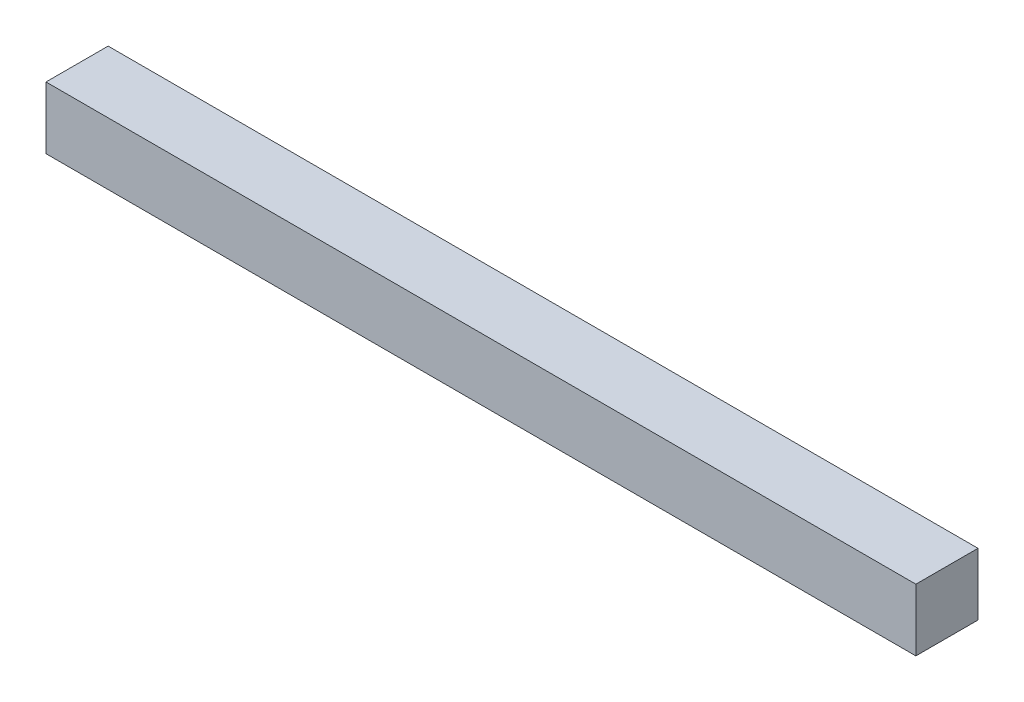
SolidWorks part; units mm, degrees
ref_plane "Front Plane" through (0, 0, 0) normal (0, 0, 1) x (1, 0, 0)
ref_plane "Top Plane" through (0, 0, 0) normal (0, 1, 0) x (1, 0, 0)
ref_plane "Right Plane" through (0, 0, 0) normal (1, 0, 0) x (0, 0, -1)
sketch "Sketch1" plane through (0, 0, 0) normal (1, 0, 0) x (0, 0, -1)
  line L1 (1.5875, -1.5875) -> (-1.5875, -1.5875)
  line L2 (1.5875, -1.5875) -> (1.5875, 1.5875)
  line L3 (1.5875, 1.5875) -> (-1.5875, 1.5875)
  line L4 (-1.5875, -1.5875) -> (-1.5875, 1.5875)
  line L5 (1.5875, -1.5875) -> (-1.5875, 1.5875) construction
  line L6 (1.5875, 1.5875) -> (-1.5875, -1.5875) construction
  point P0 (0, 0)
  dimension "D1" = 3.175
  dimension "D2" = 3.175
extrude "Boss-Extrude1" add sketch "Sketch1" along normal blind 44.45 contours L4 L3 L2 L1
